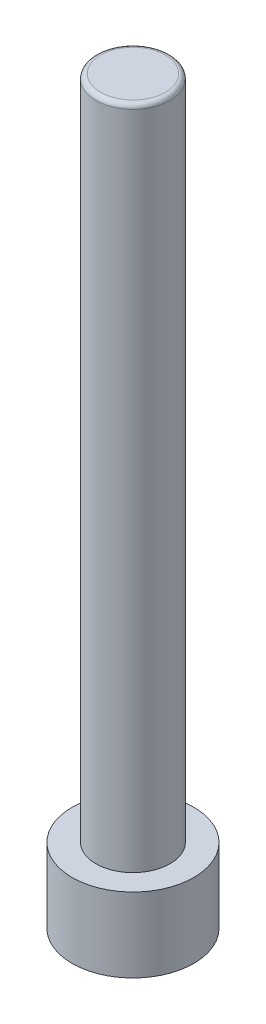
SolidWorks part; units mm, degrees
ref_plane "Front Plane" through (0, 0, 0) normal (0, 0, 1) x (1, 0, 0)
ref_plane "Top Plane" through (0, 0, 0) normal (0, 1, 0) x (1, 0, 0)
ref_plane "Right Plane" through (0, 0, 0) normal (1, 0, 0) x (0, 0, -1)
sketch "Sketch1" plane through (0, 0, 0) normal (0, 1, 0) x (1, 0, 0)
  line L1 (7.3901, 0) -> (3.695, 6.4) construction
  line L2 (3.695, 6.4) -> (-3.695, 6.4) construction
  line L3 (-3.695, 6.4) -> (-7.3901, 0) construction
  line L4 (-7.3901, 0) -> (-3.695, -6.4) construction
  line L5 (-3.695, -6.4) -> (3.695, -6.4) construction
  line L6 (3.695, -6.4) -> (7.3901, 0) construction
  circle A0 centre (0, 0) radius 6.4
  dimension "D1" = 12.8
extrude "Boss-Extrude1" add sketch "Sketch1" along normal blind 77.83
sketch "Sketch2" plane through (0, 77.83, 0) normal (0, 1, 0) x (1, 0, 0)
  circle A0 centre (0, 0) radius 3.9
  dimension "D1" = 7.8
extrude "Cut-Extrude1" cut sketch "Sketch2" against normal blind 70 flip side to cut
sketch "Sketch8" plane through (0, 0, 0) normal (0, -1, 0) x (1, 0, 0)
  line L1 (3.4641, 0) -> (1.7321, 3)
  line L2 (1.7321, 3) -> (-1.7321, 3)
  line L3 (-1.7321, 3) -> (-3.4641, 0)
  line L4 (-3.4641, 0) -> (-1.7321, -3)
  line L5 (-1.7321, -3) -> (1.7321, -3)
  line L6 (1.7321, -3) -> (3.4641, 0)
  circle A0 centre (0, 0) radius 3 construction
  dimension "D1" = 6
extrude "Cut-Extrude2" cut sketch "Sketch8" against normal blind 5.64
fillet "Fillet1" radius 0.5 1 edges at (0, 77.83, 3.9)
